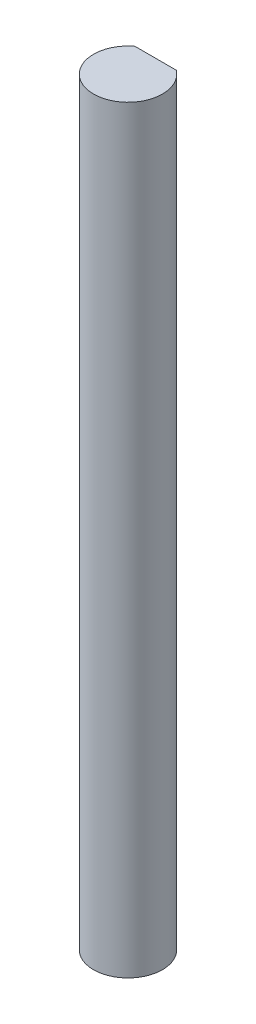
SolidWorks part; units mm, degrees
ref_plane "Front Plane" through (0, 0, 0) normal (0, 0, 1) x (1, 0, 0)
ref_plane "Top Plane" through (0, 0, 0) normal (0, 1, 0) x (1, 0, 0)
ref_plane "Right Plane" through (0, 0, 0) normal (1, 0, 0) x (0, 0, -1)
sketch "Sketch1" plane through (0, 0, 0) normal (0, 1, 0) x (1, 0, 0)
  line L0 (-1.905, 2.54) -> (1.905, 2.54)
  arc A0 (-1.905, 2.54) -> (1.905, 2.54) centre (0, 0) ccw
  dimension "D1" = 6.35
  dimension "D2" = 2.54
extrude "Boss-Extrude1" add sketch "Sketch1" along normal blind 69.85
